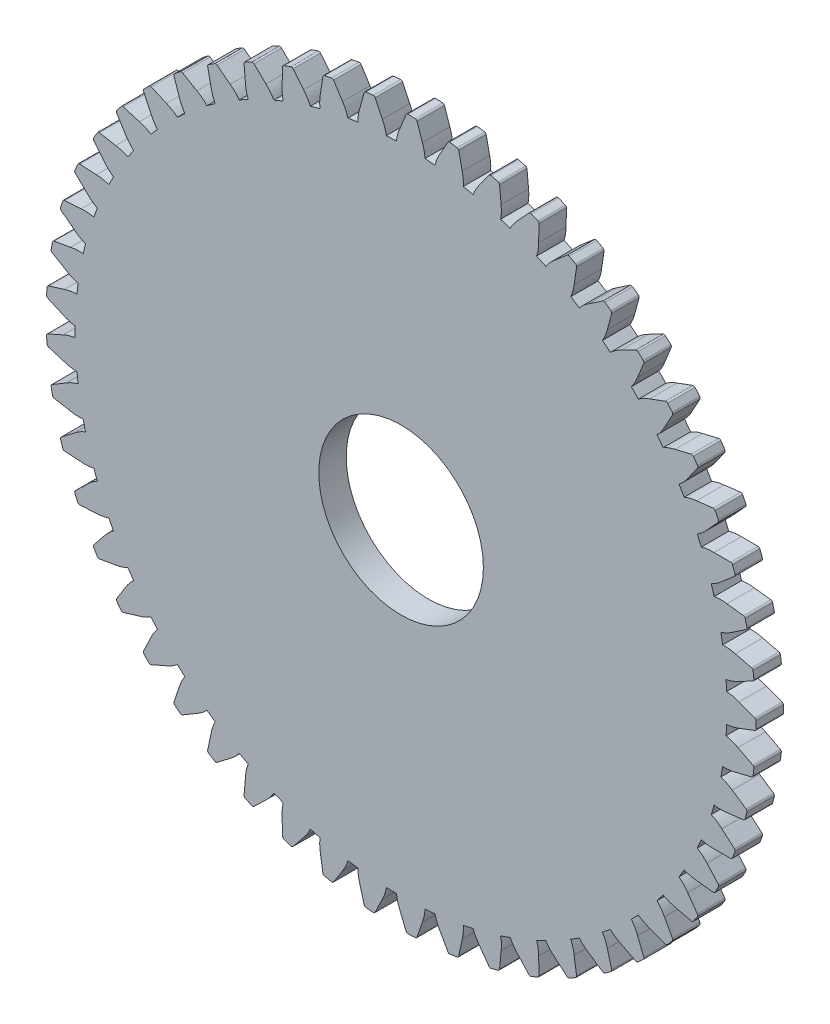
SolidWorks part; units mm, degrees
ref_plane "Front Plane" through (0, 0, 0) normal (0, 0, 1) x (1, 0, 0)
ref_plane "Top Plane" through (0, 0, 0) normal (0, 1, 0) x (1, 0, 0)
ref_plane "Right Plane" through (0, 0, 0) normal (1, 0, 0) x (0, 0, -1)
sketch "Model" plane through (0, 0, 0) normal (0, 0, 1) x (1, 0, 0)
  arc A0 (51.1069, 28.355) -> (51.0879, 28.7231) centre (27.376, 27.3159) ccw
  arc A1 (52.0104, 28.143) -> (51.1069, 28.355) centre (50.9075, 25.4735) ccw
  arc A2 (53.1489, 27.7177) -> (52.0104, 28.143) centre (-1532.1106, -4214.0875) ccw
  arc A3 (53.2463, 27.3159) -> (53.245, 27.5808) centre (27.376, 27.3159) ccw
  arc A4 (53.245, 27.5808) -> (53.1489, 27.7177) centre (53.0972, 27.5792) ccw
  arc A5 (51.0879, 25.9087) -> (51.1069, 26.2768) centre (27.376, 27.3159) ccw
  arc A6 (51.1069, 26.2768) -> (52.0104, 26.4888) centre (50.9075, 29.1583) ccw
  arc A7 (52.0104, 26.4888) -> (53.1489, 26.9141) centre (-1532.1106, 4268.7193) ccw
  arc A8 (53.245, 27.051) -> (53.2463, 27.3159) centre (27.376, 27.3159) ccw
  arc A9 (53.1489, 26.9141) -> (53.245, 27.051) centre (53.0972, 27.0525) ccw
  arc A10 (51.0633, 25.5409) -> (51.0879, 25.9087) centre (27.376, 27.3159) ccw
  arc A11 (51.9353, 25.2236) -> (51.0633, 25.5409) centre (50.5244, 22.7033) ccw
  arc A12 (53.0156, 24.6666) -> (51.9353, 25.2236) centre (-2022.8089, -3999.8721) ccw
  arc A13 (53.0647, 24.2561) -> (53.0947, 24.5193) centre (27.376, 27.3159) ccw
  arc A14 (53.0947, 24.5193) -> (53.0156, 24.6666) centre (52.9478, 24.5353) ccw
  arc A15 (50.7551, 23.1141) -> (50.8175, 23.4774) centre (27.376, 27.3159) ccw
  arc A16 (50.8175, 23.4774) -> (51.7396, 23.581) centre (50.9602, 26.3622) ccw
  arc A17 (51.7396, 23.581) -> (52.9205, 23.8687) centre (-1019.5204, 4423.3947) ccw
  arc A18 (53.0321, 23.9933) -> (53.0647, 24.2561) centre (27.376, 27.3159) ccw
  arc A19 (52.9205, 23.8687) -> (53.0321, 23.9933) centre (52.8855, 24.0123) ccw
  arc A20 (50.6871, 22.7518) -> (50.7551, 23.1141) centre (27.376, 27.3159) ccw
  arc A21 (51.5154, 22.3336) -> (50.6871, 22.7518) centre (49.8164, 19.9978) ccw
  arc A22 (52.5223, 21.6527) -> (51.5154, 22.3336) centre (-2484.7272, -3729.1238) ccw
  arc A23 (52.5226, 21.2393) -> (52.5834, 21.4971) centre (27.376, 27.3159) ccw
  arc A24 (52.5834, 21.4971) -> (52.5223, 21.6527) centre (52.4395, 21.5303) ccw
  arc A25 (50.094, 20.3785) -> (50.1989, 20.7318) centre (27.376, 27.3159) ccw
  arc A26 (50.1989, 20.7318) -> (51.1269, 20.7256) centre (50.6819, 23.5795) ccw
  arc A27 (51.1269, 20.7256) -> (52.3335, 20.8716) centre (-492.2342, 4516.3588) ccw
  arc A28 (52.459, 20.9822) -> (52.5226, 21.2393) centre (27.376, 27.3159) ccw
  arc A29 (52.3335, 20.8716) -> (52.459, 20.9822) centre (52.3157, 21.0183) ccw
  arc A30 (49.9836, 20.0268) -> (50.094, 20.3785) centre (27.376, 27.3159) ccw
  arc A31 (50.7567, 19.5135) -> (49.9836, 20.0268) centre (48.7933, 17.3951) ccw
  arc A32 (51.676, 18.7183) -> (50.7567, 19.5135) centre (-2911.381, -3405.6433) ccw
  arc A33 (51.6274, 18.3078) -> (51.7183, 18.5565) centre (27.376, 27.3159) ccw
  arc A34 (51.7183, 18.5565) -> (51.676, 18.7183) centre (51.5793, 18.6066) ccw
  arc A35 (49.1141, 17.7402) -> (49.26, 18.0787) centre (27.376, 27.3159) ccw
  arc A36 (49.26, 18.0787) -> (50.1807, 17.9628) centre (50.0764, 20.8493) ccw
  arc A37 (50.1807, 17.9628) -> (51.3962, 17.9651) centre (42.3462, 4546.3066) ccw
  arc A38 (51.5339, 18.06) -> (51.6274, 18.3078) centre (27.376, 27.3159) ccw
  arc A39 (51.3962, 17.9651) -> (51.5339, 18.06) centre (51.3959, 18.1128) ccw
  arc A40 (48.9629, 17.4041) -> (49.1141, 17.7402) centre (27.376, 27.3159) ccw
  arc A41 (49.6698, 16.8029) -> (48.9629, 17.4041) centre (47.4696, 14.9316) ccw
  arc A42 (50.4885, 15.9046) -> (49.6698, 16.8029) centre (-3296.7811, -3033.9716) ccw
  arc A43 (50.3917, 15.5027) -> (50.5115, 15.739) centre (27.376, 27.3159) ccw
  arc A44 (50.5115, 15.739) -> (50.4885, 15.9046) centre (50.3793, 15.8051) ccw
  arc A45 (47.8289, 15.2364) -> (48.0139, 15.5552) centre (27.376, 27.3159) ccw
  arc A46 (48.0139, 15.5552) -> (48.9144, 15.3313) centre (49.1522, 18.2098) ccw
  arc A47 (48.9144, 15.3313) -> (50.1216, 15.1898) centre (576.7165, 4512.8177) ccw
  arc A48 (50.2696, 15.2677) -> (50.3917, 15.5027) centre (27.376, 27.3159) ccw
  arc A49 (50.1216, 15.1898) -> (50.2696, 15.2677) centre (50.1388, 15.3365) ccw
  arc A50 (47.639, 14.9205) -> (47.8289, 15.2364) centre (27.376, 27.3159) ccw
  arc A51 (48.2699, 14.24) -> (47.639, 14.9205) centre (45.8639, 12.642) ccw
  arc A52 (48.9767, 13.2511) -> (48.2699, 14.24) centre (-3635.5173, -2619.3261) ccw
  arc A53 (48.833, 12.8635) -> (48.9798, 13.0839) centre (27.376, 27.3159) ccw
  arc A54 (48.9798, 13.0839) -> (48.9767, 13.2511) centre (48.8564, 13.1652) ccw
  arc A55 (46.2567, 12.9021) -> (46.4781, 13.1968) centre (27.376, 27.3159) ccw
  arc A56 (46.4781, 13.1968) -> (47.3458, 12.8679) centre (47.9224, 15.6982) ccw
  arc A57 (47.3458, 12.8679) -> (48.5278, 12.5847) centre (1103.3753, 4416.3621) ccw
  arc A58 (48.6839, 12.6446) -> (48.833, 12.8635) centre (27.376, 27.3159) ccw
  arc A59 (48.5278, 12.5847) -> (48.6839, 12.6446) centre (48.5622, 12.7284) ccw
  arc A60 (46.0308, 12.6109) -> (46.2567, 12.9021) centre (27.376, 27.3159) ccw
  arc A61 (46.5767, 11.8606) -> (46.0308, 12.6109) centre (43.9986, 10.5583) ccw
  arc A62 (47.1616, 10.7951) -> (46.5767, 11.8606) centre (-3922.8346, -2167.5276) ccw
  arc A63 (46.9731, 10.4271) -> (47.1449, 10.6287) centre (27.376, 27.3159) ccw
  arc A64 (47.1449, 10.6287) -> (47.1616, 10.7951) centre (47.032, 10.724) ccw
  arc A65 (44.4194, 10.7702) -> (44.6741, 11.0367) centre (27.376, 27.3159) ccw
  arc A66 (44.6741, 11.0367) -> (45.4968, 10.6075) centre (46.4041, 13.3497) ccw
  arc A67 (45.4968, 10.6075) -> (46.637, 10.1864) centre (1614.9294, 4258.294) ccw
  arc A68 (46.7991, 10.2274) -> (46.9731, 10.4271) centre (27.376, 27.3159) ccw
  arc A69 (46.637, 10.1864) -> (46.7991, 10.2274) centre (46.6882, 10.325) ccw
  arc A70 (44.1606, 10.5077) -> (44.4194, 10.7702) centre (27.376, 27.3159) ccw
  arc A71 (44.614, 9.6981) -> (44.1606, 10.5077) centre (41.8999, 8.71) ccw
  arc A72 (45.0687, 8.5709) -> (44.614, 9.6981) centre (-4154.6995, -1684.9183) ccw
  arc A73 (44.838, 8.2279) -> (45.0325, 8.4076) centre (27.376, 27.3159) ccw
  arc A74 (45.0325, 8.4076) -> (45.0687, 8.5709) centre (44.9317, 8.5157) ccw
  arc A75 (42.3429, 8.8706) -> (42.6273, 9.105) centre (27.376, 27.3159) ccw
  arc A76 (42.6273, 9.105) -> (43.3935, 8.5815) centre (44.6187, 11.1972) ccw
  arc A77 (43.3935, 8.5815) -> (44.4758, 8.0285) centre (2104.1977, 4040.8322) ccw
  arc A78 (44.6417, 8.0501) -> (44.838, 8.2279) centre (27.376, 27.3159) ccw
  arc A79 (44.4758, 8.0285) -> (44.6417, 8.0501) centre (44.5431, 8.1601) ccw
  arc A80 (42.0549, 8.6405) -> (42.3429, 8.8706) centre (27.376, 27.3159) ccw
  arc A81 (42.4093, 7.783) -> (42.0549, 8.6405) centre (39.5974, 7.1228) ccw
  arc A82 (42.7275, 6.6099) -> (42.4093, 7.783) centre (-4327.8573, -1178.2729) ccw
  arc A83 (42.4579, 6.2966) -> (42.6723, 6.4521) centre (27.376, 27.3159) ccw
  arc A84 (42.6723, 6.4521) -> (42.7275, 6.6099) centre (42.5849, 6.5712) ccw
  arc A85 (40.0562, 7.2299) -> (40.3664, 7.429) centre (27.376, 27.3159) ccw
  arc A86 (40.3664, 7.429) -> (41.0653, 6.8186) centre (42.5913, 9.2709) ccw
  arc A87 (41.0653, 6.8186) -> (42.0746, 6.1415) centre (2564.3119, 3767.0294) ccw
  arc A88 (42.2419, 6.1432) -> (42.4579, 6.2966) centre (27.376, 27.3159) ccw
  arc A89 (42.0746, 6.1415) -> (42.2419, 6.1432) centre (42.157, 6.2642) ccw
  arc A90 (39.743, 7.0355) -> (40.0562, 7.2299) centre (27.376, 27.3159) ccw
  arc A91 (39.9936, 6.142) -> (39.743, 7.0355) centre (37.1233, 5.819) ccw
  arc A92 (40.1708, 4.9396) -> (39.9936, 6.142) centre (-4439.8772, -654.7038) ccw
  arc A93 (39.866, 4.6603) -> (40.0973, 4.7894) centre (27.376, 27.3159) ccw
  arc A94 (40.0973, 4.7894) -> (40.1708, 4.9396) centre (40.0246, 4.918) ccw
  arc A95 (37.5916, 5.8711) -> (37.9231, 6.0322) centre (27.376, 27.3159) ccw
  arc A96 (37.9231, 6.0322) -> (38.5449, 5.3434) centre (40.3503, 7.598) ccw
  arc A97 (38.5449, 5.3434) -> (39.4671, 4.5516) centre (2988.8132, 3440.7292) ccw
  arc A98 (39.6334, 4.5336) -> (39.866, 4.6603) centre (27.376, 27.3159) ccw
  arc A99 (39.4671, 4.5516) -> (39.6334, 4.5336) centre (39.5634, 4.6637) ccw
  arc A100 (37.2576, 5.7152) -> (37.5916, 5.8711) centre (27.376, 27.3159) ccw
  arc A101 (37.4007, 4.7983) -> (37.2576, 5.7152) centre (34.5124, 4.8171) ccw
  arc A102 (37.4345, 3.5833) -> (37.4007, 4.7983) centre (-4489.1866, -121.5606) ccw
  arc A103 (37.0988, 3.3421) -> (37.3437, 3.4429) centre (27.376, 27.3159) ccw
  arc A104 (37.3437, 3.4429) -> (37.4345, 3.5833) centre (37.2868, 3.5792) ccw
  arc A105 (34.9836, 4.8134) -> (35.3318, 4.9341) centre (27.376, 27.3159) ccw
  arc A106 (35.3318, 4.9341) -> (35.8678, 4.1766) centre (37.9271, 6.2019) ccw
  arc A107 (35.8678, 4.1766) -> (36.6898, 3.2813) centre (3371.7424, 3066.5122) ccw
  arc A108 (36.8528, 3.2438) -> (37.0988, 3.3421) centre (27.376, 27.3159) ccw
  arc A109 (36.6898, 3.2813) -> (36.8528, 3.2438) centre (36.7987, 3.3813) ccw
  arc A110 (34.6335, 4.698) -> (34.9836, 4.8134) centre (27.376, 27.3159) ccw
  arc A111 (34.6671, 3.7707) -> (34.6335, 4.698) centre (31.8013, 4.1309) ccw
  arc A112 (34.5569, 2.5603) -> (34.6671, 3.7707) centre (-4475.0933, 413.6726) ccw
  arc A113 (34.1951, 2.3604) -> (34.4502, 2.4315) centre (27.376, 27.3159) ccw
  arc A114 (34.4502, 2.4315) -> (34.5569, 2.5603) centre (34.4098, 2.5737) ccw
  arc A115 (32.2687, 4.0715) -> (32.6288, 4.1503) centre (27.376, 27.3159) ccw
  arc A116 (32.6288, 4.1503) -> (33.0714, 3.3347) centre (35.3558, 5.1022) ccw
  arc A117 (33.0714, 3.3347) -> (33.7818, 2.3484) centre (3707.724, 2649.6316) ccw
  arc A118 (33.9392, 2.2919) -> (34.1951, 2.3604) centre (27.376, 27.3159) ccw
  arc A119 (33.7818, 2.3484) -> (33.9392, 2.2919) centre (33.9017, 2.4348) ccw
  arc A120 (31.9074, 3.9984) -> (32.2687, 4.0715) centre (27.376, 27.3159) ccw
  arc A121 (31.8312, 3.0736) -> (31.9074, 3.9984) centre (29.0281, 3.7703) ccw
  arc A122 (31.5786, 1.8847) -> (31.8312, 3.0736) centre (-4397.7953, 943.4821) ccw
  arc A123 (31.1956, 1.7291) -> (31.4574, 1.7695) centre (27.376, 27.3159) ccw
  arc A124 (31.4574, 1.7695) -> (31.5786, 1.8847) centre (31.4341, 1.9154) ccw
  arc A125 (29.4852, 3.656) -> (29.8521, 3.6916) centre (27.376, 27.3159) ccw
  arc A126 (29.8521, 3.6916) -> (30.1951, 2.8294) centre (32.6725, 4.3143) ccw
  arc A127 (30.1951, 2.8294) -> (30.7839, 1.7661) centre (3992.0416, 2195.9394) ccw
  arc A128 (30.9335, 1.6913) -> (31.1956, 1.7291) centre (27.376, 27.3159) ccw
  arc A129 (30.7839, 1.7661) -> (30.9335, 1.6913) centre (30.9131, 1.8377) ccw
  arc A130 (29.1178, 3.6261) -> (29.4852, 3.656) centre (27.376, 27.3159) ccw
  arc A131 (28.9327, 2.7168) -> (29.1178, 3.6261) centre (26.2317, 3.7401) ccw
  arc A132 (28.5413, 1.5661) -> (28.9327, 2.7168) centre (-4258.3776, 1460.4306) ccw
  arc A133 (28.1426, 1.4569) -> (28.4073, 1.4661) centre (27.376, 27.3159) ccw
  arc A134 (28.4073, 1.4661) -> (28.5413, 1.5661) centre (28.4014, 1.6137) ccw
  arc A135 (26.6721, 3.5726) -> (27.0406, 3.5646) centre (27.376, 27.3159) ccw
  arc A136 (27.0406, 3.5646) -> (27.2792, 2.6678) centre (29.9149, 3.8493) ccw
  arc A137 (27.2792, 2.6678) -> (27.7381, 1.5423) centre (4220.7039, 1711.8044) ccw
  arc A138 (27.8778, 1.4504) -> (28.1426, 1.4569) centre (27.376, 27.3159) ccw
  arc A139 (27.7381, 1.5423) -> (27.8778, 1.4504) centre (27.8749, 1.5981) ccw
  arc A140 (26.3037, 3.5864) -> (26.6721, 3.5726) centre (27.376, 27.3159) ccw
  arc A141 (26.0124, 2.7054) -> (26.3037, 3.5864) centre (23.4513, 4.0409) ccw
  arc A142 (25.4876, 1.609) -> (26.0124, 2.7054) centre (-4058.7973, 1957.2614) ccw
  arc A143 (25.0788, 1.5477) -> (25.3427, 1.5255) centre (27.376, 27.3159) ccw
  arc A144 (25.3427, 1.5255) -> (25.4876, 1.609) centre (25.3543, 1.6729) ccw
  arc A145 (23.8688, 3.8225) -> (24.2338, 3.7709) centre (27.376, 27.3159) ccw
  arc A146 (24.2338, 3.7709) -> (24.3647, 2.8522) centre (27.1216, 3.7137) ccw
  arc A147 (24.3647, 2.8522) -> (24.6872, 1.6804) centre (4390.5012, 1204.023) ccw
  arc A148 (24.8151, 1.5726) -> (25.0788, 1.5477) centre (27.376, 27.3159) ccw
  arc A149 (24.6872, 1.6804) -> (24.8151, 1.5726) centre (24.8297, 1.7196) ccw
  arc A150 (23.5047, 3.8798) -> (23.8688, 3.8225) centre (27.376, 27.3159) ccw
  arc A151 (23.1112, 3.0394) -> (23.5047, 3.8798) centre (20.7261, 4.6685) ccw
  arc A152 (22.4604, 2.0128) -> (23.1112, 3.0394) centre (-3801.856, 2427) ccw
  arc A153 (22.0472, 2.0003) -> (22.3067, 1.947) centre (27.376, 27.3159) ccw
  arc A154 (22.3067, 1.947) -> (22.4604, 2.0128) centre (22.3356, 2.0919) ccw
  arc A155 (21.1148, 4.4022) -> (21.4711, 4.3078) centre (27.376, 27.3159) ccw
  arc A156 (21.4711, 4.3078) -> (21.4924, 3.3801) centre (24.3319, 3.9095) ccw
  arc A157 (21.4924, 3.3801) -> (21.6741, 2.1783) centre (4499.0497, 679.7231) ccw
  arc A158 (21.7883, 2.0562) -> (22.0472, 2.0003) centre (27.376, 27.3159) ccw
  arc A159 (21.6741, 2.1783) -> (21.7883, 2.0562) centre (21.8202, 2.2004) ccw
  arc A160 (20.76, 4.5021) -> (21.1148, 4.4022) centre (27.376, 27.3159) ccw
  arc A161 (20.2698, 3.7142) -> (20.76, 4.5021) centre (18.0942, 5.6139) ccw
  arc A162 (19.5023, 2.7718) -> (20.2698, 3.7142) centre (-3491.1608, 2863.0522) ccw
  arc A163 (19.0905, 2.8082) -> (19.3418, 2.7247) centre (27.376, 27.3159) ccw
  arc A164 (19.3418, 2.7247) -> (19.5023, 2.7718) centre (19.3877, 2.8651) ccw
  arc A165 (18.4487, 5.3036) -> (18.7913, 5.1677) centre (27.376, 27.3159) ccw
  arc A166 (18.7913, 5.1677) -> (18.7028, 4.244) centre (21.5849, 4.4338) ccw
  arc A167 (18.7028, 4.244) -> (18.741, 3.0291) centre (4544.8257, 146.2649) ccw
  arc A168 (18.84, 2.8943) -> (19.0905, 2.8082) centre (27.376, 27.3159) ccw
  arc A169 (18.741, 3.0291) -> (18.84, 2.8943) centre (18.8887, 3.0338) ccw
  arc A170 (18.1082, 5.4448) -> (18.4487, 5.3036) centre (27.376, 27.3159) ccw
  arc A171 (17.5283, 4.7203) -> (18.1082, 5.4448) centre (15.5925, 6.8641) ccw
  arc A172 (16.6546, 3.8753) -> (17.5283, 4.7203) centre (-3131.073, 3259.297) ccw
  arc A173 (16.25, 3.9602) -> (16.4897, 3.8475) centre (27.376, 27.3159) ccw
  arc A174 (16.4897, 3.8475) -> (16.6546, 3.8753) centre (16.5519, 3.9815) ccw
  arc A175 (15.9079, 6.5139) -> (16.232, 6.3385) centre (27.376, 27.3159) ccw
  arc A176 (16.232, 6.3385) -> (16.0348, 5.4317) centre (18.9192, 5.2793) ccw
  arc A177 (16.0348, 5.4317) -> (15.9292, 4.2209) centre (4527.1867, -388.8631) ccw
  arc A178 (16.0115, 4.0753) -> (16.25, 3.9602) centre (27.376, 27.3159) ccw
  arc A179 (15.9292, 4.2209) -> (16.0115, 4.0753) centre (16.0764, 4.2081) ccw
  arc A180 (15.5864, 6.6944) -> (15.9079, 6.5139) centre (27.376, 27.3159) ccw
  arc A181 (14.9249, 6.0436) -> (15.5864, 6.6944) centre (13.2563, 8.4013) ccw
  arc A182 (13.9575, 5.3079) -> (14.9249, 6.0436) centre (-2726.6475, 3610.1718) ccw
  arc A183 (13.5657, 5.44) -> (13.7904, 5.2998) centre (27.376, 27.3159) ccw
  arc A184 (13.7904, 5.2998) -> (13.9575, 5.3079) centre (13.868, 5.4255) ccw
  arc A185 (13.528, 8.0163) -> (13.8292, 7.8038) centre (27.376, 27.3159) ccw
  arc A186 (13.8292, 7.8038) -> (13.5261, 6.9267) centre (16.3722, 6.4342) ccw
  arc A187 (13.5261, 6.9267) -> (13.278, 5.7368) centre (4446.3801, -918.1488) ccw
  arc A188 (13.3425, 5.5825) -> (13.5657, 5.44) centre (27.376, 27.3159) ccw
  arc A189 (13.278, 5.7368) -> (13.3425, 5.5825) centre (13.4227, 5.7067) ccw
  arc A190 (13.2302, 8.2335) -> (13.528, 8.0163) centre (27.376, 27.3159) ccw
  arc A191 (12.4964, 7.6655) -> (13.2302, 8.2335) centre (11.1184, 10.204) ccw
  arc A192 (11.4487, 7.0494) -> (12.4964, 7.6655) centre (-2283.5615, 3910.7511) ccw
  arc A193 (11.0754, 7.2269) -> (11.2819, 7.0611) centre (27.376, 27.3159) ccw
  arc A194 (11.2819, 7.0611) -> (11.4487, 7.0494) centre (11.3738, 7.1768) ccw
  arc A195 (11.3426, 9.7896) -> (11.6165, 9.5429) centre (27.376, 27.3159) ccw
  arc A196 (11.6165, 9.5429) -> (11.2119, 8.7078) centre (13.9797, 7.8822) ccw
  arc A197 (11.2119, 8.7078) -> (10.8247, 7.5557) centre (4303.5404, -1434.1624) ccw
  arc A198 (10.8705, 7.3949) -> (11.0754, 7.2269) centre (27.376, 27.3159) ccw
  arc A199 (10.8247, 7.5557) -> (10.8705, 7.3949) centre (10.9648, 7.5087) ccw
  arc A200 (11.0726, 10.0405) -> (11.3426, 9.7896) centre (27.376, 27.3159) ccw
  arc A201 (10.2767, 9.5633) -> (11.0726, 10.0405) centre (9.2086, 12.2469) ccw
  arc A202 (9.1635, 9.0754) -> (10.2767, 9.5633) centre (-1808.0351, 4156.8156) ccw
  arc A203 (8.8138, 9.2959) -> (8.9992, 9.1068) centre (27.376, 27.3159) ccw
  arc A204 (8.9992, 9.1068) -> (9.1635, 9.0754) centre (9.1042, 9.2108) ccw
  arc A205 (9.3823, 11.8089) -> (9.6251, 11.5316) centre (27.376, 27.3159) ccw
  arc A206 (9.6251, 11.5316) -> (9.1245, 10.7502) centre (11.7753, 9.603) ccw
  arc A207 (9.1245, 10.7502) -> (8.6038, 9.652) centre (4100.6728, -1929.6599) ccw
  arc A208 (8.6303, 9.4868) -> (8.8138, 9.2959) centre (27.376, 27.3159) ccw
  arc A209 (8.6038, 9.652) -> (8.6303, 9.4868) centre (8.7373, 9.5887) ccw
  arc A210 (9.1438, 12.09) -> (9.3823, 11.8089) centre (27.376, 27.3159) ccw
  arc A211 (8.2971, 11.7103) -> (9.1438, 12.09) centre (7.5539, 14.5014) ccw
  arc A212 (7.134, 11.3575) -> (8.2971, 11.7103) centre (-1306.7435, 4344.9109) ccw
  arc A213 (6.8128, 11.6177) -> (6.9746, 11.408) centre (27.376, 27.3159) ccw
  arc A214 (6.9746, 11.408) -> (7.134, 11.3575) centre (7.0911, 11.4989) ccw
  arc A215 (7.6745, 14.046) -> (7.8828, 13.7418) centre (27.376, 27.3159) ccw
  arc A216 (7.8828, 13.7418) -> (7.2933, 13.0252) centre (9.7898, 11.5725) ccw
  arc A217 (7.2933, 13.0252) -> (6.6464, 11.9962) centre (3840.625, -2397.6858) ccw
  arc A218 (6.6531, 11.8291) -> (6.8128, 11.6177) centre (27.376, 27.3159) ccw
  arc A219 (6.6464, 11.9962) -> (6.6531, 11.8291) centre (6.7715, 11.9176) ccw
  arc A220 (7.471, 14.3533) -> (7.6745, 14.046) centre (27.376, 27.3159) ccw
  arc A221 (6.5853, 14.0763) -> (7.471, 14.3533) centre (6.1774, 16.9358) ccw
  arc A222 (5.3886, 13.8636) -> (6.5853, 14.0763) centre (-786.7238, 4472.3966) ccw
  arc A223 (5.1004, 14.16) -> (5.2363, 13.9326) centre (27.376, 27.3159) ccw
  arc A224 (5.2363, 13.9326) -> (5.3886, 13.8636) centre (5.3628, 14.0091) ccw
  arc A225 (6.2433, 16.4693) -> (6.4142, 16.1426) centre (27.376, 27.3159) ccw
  arc A226 (6.4142, 16.1426) -> (5.7441, 15.5007) centre (8.0512, 13.763) ccw
  arc A227 (5.7441, 15.5007) -> (4.98, 14.5555) centre (3527.0475, -2831.67) ccw
  arc A228 (4.9669, 14.3887) -> (5.1004, 14.16) centre (27.376, 27.3159) ccw
  arc A229 (4.98, 14.5555) -> (4.9669, 14.3887) centre (5.0949, 14.4626) ccw
  arc A230 (6.0775, 16.7985) -> (6.2433, 16.4693) centre (27.376, 27.3159) ccw
  arc A231 (5.1653, 16.6283) -> (6.0775, 16.7985) centre (5.0985, 19.5159) ccw
  arc A232 (3.9519, 16.5585) -> (5.1653, 16.6283) centre (-255.2759, 4537.4832) ccw
  arc A233 (3.7008, 16.8869) -> (3.8088, 16.6451) centre (27.376, 27.3159) ccw
  arc A234 (3.8088, 16.6451) -> (3.9519, 16.5585) centre (3.9434, 16.706) ccw
  arc A235 (5.1088, 19.0448) -> (5.2398, 18.7003) centre (27.376, 27.3159) ccw
  arc A236 (5.2398, 18.7003) -> (4.4985, 18.1421) centre (6.5839, 16.1437) ccw
  arc A237 (4.4985, 18.1421) -> (3.628, 17.2939) centre (3164.3423, -3225.5203) ccw
  arc A238 (3.5953, 17.1299) -> (3.7008, 16.8869) centre (27.376, 27.3159) ccw
  arc A239 (3.628, 17.2939) -> (3.5953, 17.1299) centre (3.7311, 17.1881) ccw
  arc A240 (4.9831, 19.3913) -> (5.1088, 19.0448) centre (27.376, 27.3159) ccw
  arc A241 (4.0572, 19.3302) -> (4.9831, 19.3913) centre (4.3323, 22.2054) ccw
  arc A242 (2.844, 19.4045) -> (4.0572, 19.3302) centre (280.1398, 4539.2569) ccw
  arc A243 (2.6335, 19.7603) -> (2.7122, 19.5073) centre (27.376, 27.3159) ccw
  arc A244 (2.7122, 19.5073) -> (2.844, 19.4045) centre (2.853, 19.552) ccw
  arc A245 (4.2868, 21.7365) -> (4.3762, 21.3789) centre (27.376, 27.3159) ccw
  arc A246 (4.3762, 21.3789) -> (3.574, 20.9123) centre (5.4085, 18.6813) ccw
  arc A247 (3.574, 20.9123) -> (2.6093, 20.173) centre (2757.601, -3573.7079) ccw
  arc A248 (2.5575, 20.014) -> (2.6335, 19.7603) centre (27.376, 27.3159) ccw
  arc A249 (2.6093, 20.173) -> (2.5575, 20.014) centre (2.6992, 20.0557) ccw
  arc A250 (4.203, 22.0954) -> (4.2868, 21.7365) centre (27.376, 27.3159) ccw
  arc A251 (3.2763, 22.1442) -> (4.203, 22.0954) centre (3.8896, 24.9668) ccw
  arc A252 (2.0805, 22.3615) -> (3.2763, 22.1442) centre (812.0073, 4477.6928) ccw
  arc A253 (1.9135, 22.7397) -> (1.9617, 22.4792) centre (27.376, 27.3159) ccw
  arc A254 (1.9617, 22.4792) -> (2.0805, 22.3615) centre (2.1069, 22.5068) ccw
  arc A255 (3.789, 24.5065) -> (3.8354, 24.1408) centre (27.376, 27.3159) ccw
  arc A256 (3.8354, 24.1408) -> (2.9837, 23.7724) centre (4.5414, 21.34) ccw
  arc A257 (2.9837, 23.7724) -> (1.9383, 23.1523) centre (2312.5333, -3871.3451) ccw
  arc A258 (1.868, 23.0006) -> (1.9135, 22.7397) centre (27.376, 27.3159) ccw
  arc A259 (1.9383, 23.1523) -> (1.868, 23.0006) centre (2.0137, 23.0252) ccw
  arc A260 (3.7482, 24.8728) -> (3.789, 24.5065) centre (27.376, 27.3159) ccw
  arc A261 (2.8338, 25.0309) -> (3.7482, 24.8728) centre (3.7766, 27.7611) ccw
  arc A262 (1.672, 25.388) -> (2.8338, 25.0309) centre (1332.8602, 4353.6552) ccw
  arc A263 (1.551, 25.7833) -> (1.5681, 25.519) centre (27.376, 27.3159) ccw
  arc A264 (1.5681, 25.519) -> (1.672, 25.388) centre (1.7155, 25.5293) ccw
  arc A265 (3.6223, 27.3159) -> (3.6251, 26.9473) centre (27.376, 27.3159) ccw
  arc A266 (3.6251, 26.9473) -> (2.7358, 26.6822) centre (3.9949, 24.0827) ccw
  arc A267 (2.7358, 26.6822) -> (1.6244, 26.1901) centre (1835.387, -4114.2535) ccw
  arc A268 (1.5367, 26.0478) -> (1.551, 25.7833) centre (27.376, 27.3159) ccw
  arc A269 (1.6244, 26.1901) -> (1.5367, 26.0478) centre (1.6843, 26.055) ccw
  arc A270 (3.6251, 27.6845) -> (3.6223, 27.3159) centre (27.376, 27.3159) ccw
  arc A271 (2.7358, 27.9496) -> (3.6251, 27.6845) centre (3.9949, 30.5491) ccw
  arc A272 (1.6244, 28.4416) -> (2.7358, 27.9496) centre (1835.387, 4168.8853) ccw
  arc A273 (1.551, 28.8485) -> (1.5367, 28.584) centre (27.376, 27.3159) ccw
  arc A274 (1.5367, 28.584) -> (1.6244, 28.4416) centre (1.6843, 28.5767) ccw
  arc A275 (3.789, 30.1253) -> (3.7482, 29.759) centre (27.376, 27.3159) ccw
  arc A276 (3.7482, 29.759) -> (2.8338, 29.6009) centre (3.7766, 26.8707) ccw
  arc A277 (2.8338, 29.6009) -> (1.672, 29.2438) centre (1332.8602, -4299.0235) ccw
  arc A278 (1.5681, 29.1128) -> (1.551, 28.8485) centre (27.376, 27.3159) ccw
  arc A279 (1.672, 29.2438) -> (1.5681, 29.1128) centre (1.7155, 29.1025) ccw
  arc A280 (3.8354, 30.491) -> (3.789, 30.1253) centre (27.376, 27.3159) ccw
  arc A281 (2.9837, 30.8594) -> (3.8354, 30.491) centre (4.5414, 33.2917) ccw
  arc A282 (1.9383, 31.4794) -> (2.9837, 30.8594) centre (2312.5333, 3925.9768) ccw
  arc A283 (1.9135, 31.8921) -> (1.868, 31.6312) centre (27.376, 27.3159) ccw
  arc A284 (1.868, 31.6312) -> (1.9383, 31.4794) centre (2.0137, 31.6065) ccw
  arc A285 (4.2868, 32.8953) -> (4.203, 32.5364) centre (27.376, 27.3159) ccw
  arc A286 (4.203, 32.5364) -> (3.2763, 32.4875) centre (3.8896, 29.665) ccw
  arc A287 (3.2763, 32.4875) -> (2.0805, 32.2703) centre (812.0073, -4423.0611) ccw
  arc A288 (1.9617, 32.1526) -> (1.9135, 31.8921) centre (27.376, 27.3159) ccw
  arc A289 (2.0805, 32.2703) -> (1.9617, 32.1526) centre (2.1069, 32.1249) ccw
  arc A290 (4.3762, 33.2529) -> (4.2868, 32.8953) centre (27.376, 27.3159) ccw
  arc A291 (3.574, 33.7195) -> (4.3762, 33.2529) centre (5.4085, 35.9505) ccw
  arc A292 (2.6093, 34.4588) -> (3.574, 33.7195) centre (2757.601, 3628.3397) ccw
  arc A293 (2.6335, 34.8715) -> (2.5575, 34.6178) centre (27.376, 27.3159) ccw
  arc A294 (2.5575, 34.6178) -> (2.6093, 34.4588) centre (2.6992, 34.5761) ccw
  arc A295 (5.1088, 35.587) -> (4.9831, 35.2404) centre (27.376, 27.3159) ccw
  arc A296 (4.9831, 35.2404) -> (4.0572, 35.3016) centre (4.3323, 32.4263) ccw
  arc A297 (4.0572, 35.3016) -> (2.844, 35.2273) centre (280.1398, -4484.6251) ccw
  arc A298 (2.7122, 35.1244) -> (2.6335, 34.8715) centre (27.376, 27.3159) ccw
  arc A299 (2.844, 35.2273) -> (2.7122, 35.1244) centre (2.853, 35.0798) ccw
  arc A300 (5.2398, 35.9315) -> (5.1088, 35.587) centre (27.376, 27.3159) ccw
  arc A301 (4.4985, 36.4897) -> (5.2398, 35.9315) centre (6.5839, 38.4881) ccw
  arc A302 (3.628, 37.3379) -> (4.4985, 36.4897) centre (3164.3423, 3280.1521) ccw
  arc A303 (3.7008, 37.7448) -> (3.5953, 37.5019) centre (27.376, 27.3159) ccw
  arc A304 (3.5953, 37.5019) -> (3.628, 37.3379) centre (3.7311, 37.4437) ccw
  arc A305 (6.2433, 38.1625) -> (6.0775, 37.8333) centre (27.376, 27.3159) ccw
  arc A306 (6.0775, 37.8333) -> (5.1653, 38.0035) centre (5.0985, 35.1159) ccw
  arc A307 (5.1653, 38.0035) -> (3.9519, 38.0733) centre (-255.2759, -4482.8514) ccw
  arc A308 (3.8088, 37.9867) -> (3.7008, 37.7448) centre (27.376, 27.3159) ccw
  arc A309 (3.9519, 38.0733) -> (3.8088, 37.9867) centre (3.9434, 37.9257) ccw
  arc A310 (6.4142, 38.4891) -> (6.2433, 38.1625) centre (27.376, 27.3159) ccw
  arc A311 (5.7441, 39.1311) -> (6.4142, 38.4891) centre (8.0512, 40.8688) ccw
  arc A312 (4.98, 40.0763) -> (5.7441, 39.1311) centre (3527.0475, 2886.3018) ccw
  arc A313 (5.1004, 40.4718) -> (4.9669, 40.243) centre (27.376, 27.3159) ccw
  arc A314 (4.9669, 40.243) -> (4.98, 40.0763) centre (5.0949, 40.1692) ccw
  arc A315 (7.6745, 40.5858) -> (7.471, 40.2785) centre (27.376, 27.3159) ccw
  arc A316 (7.471, 40.2785) -> (6.5853, 40.5554) centre (6.1774, 37.696) ccw
  arc A317 (6.5853, 40.5554) -> (5.3886, 40.7682) centre (-786.7238, -4417.7649) ccw
  arc A318 (5.2363, 40.6991) -> (5.1004, 40.4718) centre (27.376, 27.3159) ccw
  arc A319 (5.3886, 40.7682) -> (5.2363, 40.6991) centre (5.3628, 40.6227) ccw
  arc A320 (7.8828, 40.8899) -> (7.6745, 40.5858) centre (27.376, 27.3159) ccw
  arc A321 (7.2933, 41.6066) -> (7.8828, 40.8899) centre (9.7898, 43.0593) ccw
  arc A322 (6.6464, 42.6356) -> (7.2933, 41.6066) centre (3840.625, 2452.3176) ccw
  arc A323 (6.8128, 43.014) -> (6.6531, 42.8027) centre (27.376, 27.3159) ccw
  arc A324 (6.6531, 42.8027) -> (6.6464, 42.6356) centre (6.7715, 42.7142) ccw
  arc A325 (9.3823, 42.8228) -> (9.1438, 42.5418) centre (27.376, 27.3159) ccw
  arc A326 (9.1438, 42.5418) -> (8.2971, 42.9215) centre (7.5539, 40.1304) ccw
  arc A327 (8.2971, 42.9215) -> (7.134, 43.2743) centre (-1306.7435, -4290.2791) ccw
  arc A328 (6.9746, 43.2237) -> (6.8128, 43.014) centre (27.376, 27.3159) ccw
  arc A329 (7.134, 43.2743) -> (6.9746, 43.2237) centre (7.0911, 43.1329) ccw
  arc A330 (9.6251, 43.1002) -> (9.3823, 42.8228) centre (27.376, 27.3159) ccw
  arc A331 (9.1245, 43.8815) -> (9.6251, 43.1002) centre (11.7753, 45.0287) ccw
  arc A332 (8.6038, 44.9798) -> (9.1245, 43.8815) centre (4100.6728, 1984.2917) ccw
  arc A333 (8.8138, 45.3359) -> (8.6303, 45.1449) centre (27.376, 27.3159) ccw
  arc A334 (8.6303, 45.1449) -> (8.6038, 44.9798) centre (8.7373, 45.0431) ccw
  arc A335 (11.3426, 44.8422) -> (11.0726, 44.5913) centre (27.376, 27.3159) ccw
  arc A336 (11.0726, 44.5913) -> (10.2767, 45.0685) centre (9.2086, 42.3848) ccw
  arc A337 (10.2767, 45.0685) -> (9.1635, 45.5564) centre (-1808.0351, -4102.1838) ccw
  arc A338 (8.9992, 45.525) -> (8.8138, 45.3359) centre (27.376, 27.3159) ccw
  arc A339 (9.1635, 45.5564) -> (8.9992, 45.525) centre (9.1042, 45.421) ccw
  arc A340 (11.6165, 45.0888) -> (11.3426, 44.8422) centre (27.376, 27.3159) ccw
  arc A341 (11.2119, 45.9239) -> (11.6165, 45.0888) centre (13.9797, 46.7495) ccw
  arc A342 (10.8247, 47.0761) -> (11.2119, 45.9239) centre (4303.5404, 1488.7941) ccw
  arc A343 (11.0754, 47.4048) -> (10.8705, 47.2369) centre (27.376, 27.3159) ccw
  arc A344 (10.8705, 47.2369) -> (10.8247, 47.0761) centre (10.9648, 47.1231) ccw
  arc A345 (13.528, 46.6155) -> (13.2302, 46.3983) centre (27.376, 27.3159) ccw
  arc A346 (13.2302, 46.3983) -> (12.4964, 46.9662) centre (11.1184, 44.4278) ccw
  arc A347 (12.4964, 46.9662) -> (11.4487, 47.5824) centre (-2283.5615, -3856.1193) ccw
  arc A348 (11.2819, 47.5707) -> (11.0754, 47.4048) centre (27.376, 27.3159) ccw
  arc A349 (11.4487, 47.5824) -> (11.2819, 47.5707) centre (11.3738, 47.455) ccw
  arc A350 (13.8292, 46.828) -> (13.528, 46.6155) centre (27.376, 27.3159) ccw
  arc A351 (13.5261, 47.7051) -> (13.8292, 46.828) centre (16.3722, 48.1976) ccw
  arc A352 (13.278, 48.8949) -> (13.5261, 47.7051) centre (4446.3801, 972.7806) ccw
  arc A353 (13.5657, 49.1918) -> (13.3425, 49.0492) centre (27.376, 27.3159) ccw
  arc A354 (13.3425, 49.0492) -> (13.278, 48.8949) centre (13.4227, 48.9251) ccw
  arc A355 (15.9079, 48.1178) -> (15.5864, 47.9374) centre (27.376, 27.3159) ccw
  arc A356 (15.5864, 47.9374) -> (14.9249, 48.5882) centre (13.2563, 46.2305) ccw
  arc A357 (14.9249, 48.5882) -> (13.9575, 49.3239) centre (-2726.6475, -3555.54) ccw
  arc A358 (13.7904, 49.332) -> (13.5657, 49.1918) centre (27.376, 27.3159) ccw
  arc A359 (13.9575, 49.3239) -> (13.7904, 49.332) centre (13.868, 49.2063) ccw
  arc A360 (16.232, 48.2933) -> (15.9079, 48.1178) centre (27.376, 27.3159) ccw
  arc A361 (16.0348, 49.2001) -> (16.232, 48.2933) centre (18.9192, 49.3524) ccw
  arc A362 (15.9292, 50.4109) -> (16.0348, 49.2001) centre (4527.1867, 443.4949) ccw
  arc A363 (16.25, 50.6716) -> (16.0115, 50.5565) centre (27.376, 27.3159) ccw
  arc A364 (16.0115, 50.5565) -> (15.9292, 50.4109) centre (16.0764, 50.4237) ccw
  arc A365 (18.4487, 49.3282) -> (18.1082, 49.187) centre (27.376, 27.3159) ccw
  arc A366 (18.1082, 49.187) -> (17.5283, 49.9115) centre (15.5925, 47.7677) ccw
  arc A367 (17.5283, 49.9115) -> (16.6546, 50.7565) centre (-3131.073, -3204.6652) ccw
  arc A368 (16.4897, 50.7843) -> (16.25, 50.6716) centre (27.376, 27.3159) ccw
  arc A369 (16.6546, 50.7565) -> (16.4897, 50.7843) centre (16.5519, 50.6502) ccw
  arc A370 (18.7913, 49.4641) -> (18.4487, 49.3282) centre (27.376, 27.3159) ccw
  arc A371 (18.7028, 50.3878) -> (18.7913, 49.4641) centre (21.5849, 50.198) ccw
  arc A372 (18.741, 51.6026) -> (18.7028, 50.3878) centre (4544.8257, -91.6331) ccw
  arc A373 (19.0905, 51.8236) -> (18.84, 51.7375) centre (27.376, 27.3159) ccw
  arc A374 (18.84, 51.7375) -> (18.741, 51.6026) centre (18.8887, 51.598) ccw
  arc A375 (21.1148, 50.2296) -> (20.76, 50.1296) centre (27.376, 27.3159) ccw
  arc A376 (20.76, 50.1296) -> (20.2698, 50.9176) centre (18.0942, 49.0178) ccw
  arc A377 (20.2698, 50.9176) -> (19.5023, 51.86) centre (-3491.1608, -2808.4204) ccw
  arc A378 (19.3418, 51.9071) -> (19.0905, 51.8236) centre (27.376, 27.3159) ccw
  arc A379 (19.5023, 51.86) -> (19.3418, 51.9071) centre (19.3877, 51.7666) ccw
  arc A380 (21.4711, 50.324) -> (21.1148, 50.2296) centre (27.376, 27.3159) ccw
  arc A381 (21.4924, 51.2517) -> (21.4711, 50.324) centre (24.3319, 50.7223) ccw
  arc A382 (21.6741, 52.4534) -> (21.4924, 51.2517) centre (4499.0497, -625.0914) ccw
  arc A383 (22.0472, 52.6315) -> (21.7883, 52.5756) centre (27.376, 27.3159) ccw
  arc A384 (21.7883, 52.5756) -> (21.6741, 52.4534) centre (21.8202, 52.4313) ccw
  arc A385 (23.8688, 50.8093) -> (23.5047, 50.752) centre (27.376, 27.3159) ccw
  arc A386 (23.5047, 50.752) -> (23.1112, 51.5924) centre (20.7261, 49.9633) ccw
  arc A387 (23.1112, 51.5924) -> (22.4604, 52.619) centre (-3801.856, -2372.3682) ccw
  arc A388 (22.3067, 52.6847) -> (22.0472, 52.6315) centre (27.376, 27.3159) ccw
  arc A389 (22.4604, 52.619) -> (22.3067, 52.6847) centre (22.3356, 52.5398) ccw
  arc A390 (24.2338, 50.8608) -> (23.8688, 50.8093) centre (27.376, 27.3159) ccw
  arc A391 (24.3647, 51.7795) -> (24.2338, 50.8608) centre (27.1216, 50.918) ccw
  arc A392 (24.6872, 52.9514) -> (24.3647, 51.7795) centre (4390.5012, -1149.3912) ccw
  arc A393 (25.0788, 53.0841) -> (24.8151, 53.0592) centre (27.376, 27.3159) ccw
  arc A394 (24.8151, 53.0592) -> (24.6872, 52.9514) centre (24.8297, 52.9122) ccw
  arc A395 (26.6721, 51.0592) -> (26.3037, 51.0454) centre (27.376, 27.3159) ccw
  arc A396 (26.3037, 51.0454) -> (26.0124, 51.9264) centre (23.4513, 50.5908) ccw
  arc A397 (26.0124, 51.9264) -> (25.4876, 53.0227) centre (-4058.7973, -1902.6296) ccw
  arc A398 (25.3427, 53.1062) -> (25.0788, 53.0841) centre (27.376, 27.3159) ccw
  arc A399 (25.4876, 53.0227) -> (25.3427, 53.1062) centre (25.3543, 52.9589) ccw
  arc A400 (27.0406, 51.0672) -> (26.6721, 51.0592) centre (27.376, 27.3159) ccw
  arc A401 (27.2792, 51.964) -> (27.0406, 51.0672) centre (29.9149, 50.7825) ccw
  arc A402 (27.7381, 53.0895) -> (27.2792, 51.964) centre (4220.7039, -1657.1727) ccw
  arc A403 (28.1426, 53.1749) -> (27.8778, 53.1814) centre (27.376, 27.3159) ccw
  arc A404 (27.8778, 53.1814) -> (27.7381, 53.0895) centre (27.8749, 53.0336) ccw
  arc A405 (29.4852, 50.9758) -> (29.1178, 51.0056) centre (27.376, 27.3159) ccw
  arc A406 (29.1178, 51.0056) -> (28.9327, 51.915) centre (26.2317, 50.8917) ccw
  arc A407 (28.9327, 51.915) -> (28.5413, 53.0656) centre (-4258.3776, -1405.7989) ccw
  arc A408 (28.4073, 53.1657) -> (28.1426, 53.1749) centre (27.376, 27.3159) ccw
  arc A409 (28.5413, 53.0656) -> (28.4073, 53.1657) centre (28.4014, 53.018) ccw
  arc A410 (29.8521, 50.9402) -> (29.4852, 50.9758) centre (27.376, 27.3159) ccw
  arc A411 (30.1951, 51.8024) -> (29.8521, 50.9402) centre (32.6725, 50.3175) ccw
  arc A412 (30.7839, 52.8657) -> (30.1951, 51.8024) centre (3992.0416, -2141.3076) ccw
  arc A413 (31.1956, 52.9027) -> (30.9335, 52.9405) centre (27.376, 27.3159) ccw
  arc A414 (30.9335, 52.9405) -> (30.7839, 52.8657) centre (30.9131, 52.7941) ccw
  arc A415 (32.2687, 50.5602) -> (31.9074, 50.6334) centre (27.376, 27.3159) ccw
  arc A416 (31.9074, 50.6334) -> (31.8312, 51.5582) centre (29.0281, 50.8615) ccw
  arc A417 (31.8312, 51.5582) -> (31.5786, 52.7471) centre (-4397.7953, -888.8503) ccw
  arc A418 (31.4574, 52.8623) -> (31.1956, 52.9027) centre (27.376, 27.3159) ccw
  arc A419 (31.5786, 52.7471) -> (31.4574, 52.8623) centre (31.4341, 52.7164) ccw
  arc A420 (32.6288, 50.4815) -> (32.2687, 50.5602) centre (27.376, 27.3159) ccw
  arc A421 (33.0714, 51.2971) -> (32.6288, 50.4815) centre (35.3558, 49.5296) ccw
  arc A422 (33.7818, 52.2833) -> (33.0714, 51.2971) centre (3707.724, -2594.9998) ccw
  arc A423 (34.1951, 52.2714) -> (33.9392, 52.3399) centre (27.376, 27.3159) ccw
  arc A424 (33.9392, 52.3399) -> (33.7818, 52.2833) centre (33.9017, 52.1969) ccw
  arc A425 (34.9836, 49.8184) -> (34.6335, 49.9337) centre (27.376, 27.3159) ccw
  arc A426 (34.6335, 49.9337) -> (34.6671, 50.8611) centre (31.8013, 50.5009) ccw
  arc A427 (34.6671, 50.8611) -> (34.5569, 52.0715) centre (-4475.0933, -359.0408) ccw
  arc A428 (34.4502, 52.2002) -> (34.1951, 52.2714) centre (27.376, 27.3159) ccw
  arc A429 (34.5569, 52.0715) -> (34.4502, 52.2002) centre (34.4098, 52.0581) ccw
  arc A430 (35.3318, 49.6976) -> (34.9836, 49.8184) centre (27.376, 27.3159) ccw
  arc A431 (35.8678, 50.4552) -> (35.3318, 49.6976) centre (37.9271, 48.4299) ccw
  arc A432 (36.6898, 51.3504) -> (35.8678, 50.4552) centre (3371.7424, -3011.8805) ccw
  arc A433 (37.0988, 51.2897) -> (36.8528, 51.388) centre (27.376, 27.3159) ccw
  arc A434 (36.8528, 51.388) -> (36.6898, 51.3504) centre (36.7987, 51.2505) ccw
  arc A435 (37.5916, 48.7607) -> (37.2576, 48.9166) centre (27.376, 27.3159) ccw
  arc A436 (37.2576, 48.9166) -> (37.4007, 49.8335) centre (34.5124, 49.8147) ccw
  arc A437 (37.4007, 49.8335) -> (37.4345, 51.0484) centre (-4489.1866, 176.1923) ccw
  arc A438 (37.3437, 51.1889) -> (37.0988, 51.2897) centre (27.376, 27.3159) ccw
  arc A439 (37.4345, 51.0484) -> (37.3437, 51.1889) centre (37.2868, 51.0525) ccw
  arc A440 (37.9231, 48.5996) -> (37.5916, 48.7607) centre (27.376, 27.3159) ccw
  arc A441 (38.5449, 49.2884) -> (37.9231, 48.5996) centre (40.3503, 47.0337) ccw
  arc A442 (39.4671, 50.0802) -> (38.5449, 49.2884) centre (2988.8132, -3386.0975) ccw
  arc A443 (39.866, 49.9715) -> (39.6334, 50.0982) centre (27.376, 27.3159) ccw
  arc A444 (39.6334, 50.0982) -> (39.4671, 50.0802) centre (39.5634, 49.968) ccw
  arc A445 (40.0562, 47.4019) -> (39.743, 47.5963) centre (27.376, 27.3159) ccw
  arc A446 (39.743, 47.5963) -> (39.9936, 48.4898) centre (37.1233, 48.8128) ccw
  arc A447 (39.9936, 48.4898) -> (40.1708, 49.6922) centre (-4439.8772, 709.3355) ccw
  arc A448 (40.0973, 49.8424) -> (39.866, 49.9715) centre (27.376, 27.3159) ccw
  arc A449 (40.1708, 49.6922) -> (40.0973, 49.8424) centre (40.0246, 49.7137) ccw
  arc A450 (40.3664, 47.2027) -> (40.0562, 47.4019) centre (27.376, 27.3159) ccw
  arc A451 (41.0653, 47.8132) -> (40.3664, 47.2027) centre (42.5913, 45.3608) ccw
  arc A452 (42.0746, 48.4903) -> (41.0653, 47.8132) centre (2564.3119, -3712.3976) ccw
  arc A453 (42.4579, 48.3352) -> (42.2419, 48.4885) centre (27.376, 27.3159) ccw
  arc A454 (42.2419, 48.4885) -> (42.0746, 48.4903) centre (42.157, 48.3676) ccw
  arc A455 (42.3429, 45.7612) -> (42.0549, 45.9912) centre (27.376, 27.3159) ccw
  arc A456 (42.0549, 45.9912) -> (42.4093, 46.8488) centre (39.5974, 47.509) ccw
  arc A457 (42.4093, 46.8488) -> (42.7275, 48.0219) centre (-4327.8573, 1232.9047) ccw
  arc A458 (42.6723, 48.1797) -> (42.4579, 48.3352) centre (27.376, 27.3159) ccw
  arc A459 (42.7275, 48.0219) -> (42.6723, 48.1797) centre (42.5849, 48.0605) ccw
  arc A460 (42.6273, 45.5267) -> (42.3429, 45.7612) centre (27.376, 27.3159) ccw
  arc A461 (43.3935, 46.0503) -> (42.6273, 45.5267) centre (44.6187, 43.4346) ccw
  arc A462 (44.4758, 46.6032) -> (43.3935, 46.0503) centre (2104.1977, -3986.2004) ccw
  arc A463 (44.838, 46.4039) -> (44.6417, 46.5817) centre (27.376, 27.3159) ccw
  arc A464 (44.6417, 46.5817) -> (44.4758, 46.6032) centre (44.5431, 46.4716) ccw
  arc A465 (44.4194, 43.8616) -> (44.1606, 44.124) centre (27.376, 27.3159) ccw
  arc A466 (44.1606, 44.124) -> (44.614, 44.9337) centre (41.8999, 45.9218) ccw
  arc A467 (44.614, 44.9337) -> (45.0687, 46.0609) centre (-4154.6995, 1739.55) ccw
  arc A468 (45.0325, 46.2241) -> (44.838, 46.4039) centre (27.376, 27.3159) ccw
  arc A469 (45.0687, 46.0609) -> (45.0325, 46.2241) centre (44.9317, 46.1161) ccw
  arc A470 (44.6741, 43.5951) -> (44.4194, 43.8616) centre (27.376, 27.3159) ccw
  arc A471 (45.4968, 44.0243) -> (44.6741, 43.5951) centre (46.4041, 41.2821) ccw
  arc A472 (46.637, 44.4454) -> (45.4968, 44.0243) centre (1614.9294, -4203.6622) ccw
  arc A473 (46.9731, 44.2046) -> (46.7991, 44.4044) centre (27.376, 27.3159) ccw
  arc A474 (46.7991, 44.4044) -> (46.637, 44.4454) centre (46.6882, 44.3068) ccw
  arc A475 (46.2567, 41.7296) -> (46.0308, 42.0209) centre (27.376, 27.3159) ccw
  arc A476 (46.0308, 42.0209) -> (46.5767, 42.7712) centre (43.9986, 44.0734) ccw
  arc A477 (46.5767, 42.7712) -> (47.1616, 43.8367) centre (-3922.8346, 2222.1594) ccw
  arc A478 (47.1449, 44.0031) -> (46.9731, 44.2046) centre (27.376, 27.3159) ccw
  arc A479 (47.1616, 43.8367) -> (47.1449, 44.0031) centre (47.032, 43.9078) ccw
  arc A480 (46.4781, 41.4349) -> (46.2567, 41.7296) centre (27.376, 27.3159) ccw
  arc A481 (47.3458, 41.7638) -> (46.4781, 41.4349) centre (47.9224, 38.9336) ccw
  arc A482 (48.5278, 42.0471) -> (47.3458, 41.7638) centre (1103.3753, -4361.7303) ccw
  arc A483 (48.833, 41.7683) -> (48.6839, 41.9872) centre (27.376, 27.3159) ccw
  arc A484 (48.6839, 41.9872) -> (48.5278, 42.0471) centre (48.5622, 41.9034) ccw
  arc A485 (47.8289, 39.3954) -> (47.639, 39.7113) centre (27.376, 27.3159) ccw
  arc A486 (47.639, 39.7113) -> (48.2699, 40.3918) centre (45.8639, 41.9898) ccw
  arc A487 (48.2699, 40.3918) -> (48.9767, 41.3806) centre (-3635.5173, 2673.9579) ccw
  arc A488 (48.9798, 41.5478) -> (48.833, 41.7683) centre (27.376, 27.3159) ccw
  arc A489 (48.9767, 41.3806) -> (48.9798, 41.5478) centre (48.8564, 41.4666) ccw
  arc A490 (48.0139, 39.0766) -> (47.8289, 39.3954) centre (27.376, 27.3159) ccw
  arc A491 (48.9144, 39.3005) -> (48.0139, 39.0766) centre (49.1522, 36.4219) ccw
  arc A492 (50.1216, 39.442) -> (48.9144, 39.3005) centre (576.7165, -4458.1859) ccw
  arc A493 (50.3917, 39.1291) -> (50.2696, 39.3641) centre (27.376, 27.3159) ccw
  arc A494 (50.2696, 39.3641) -> (50.1216, 39.442) centre (50.1388, 39.2953) ccw
  arc A495 (49.1141, 36.8916) -> (48.9629, 37.2277) centre (27.376, 27.3159) ccw
  arc A496 (48.9629, 37.2277) -> (49.6698, 37.8288) centre (47.4696, 39.7002) ccw
  arc A497 (49.6698, 37.8288) -> (50.4885, 38.7271) centre (-3296.7811, 3088.6034) ccw
  arc A498 (50.5115, 38.8928) -> (50.3917, 39.1291) centre (27.376, 27.3159) ccw
  arc A499 (50.4885, 38.7271) -> (50.5115, 38.8928) centre (50.3793, 38.8267) ccw
  arc A500 (49.26, 36.5531) -> (49.1141, 36.8916) centre (27.376, 27.3159) ccw
  arc A501 (50.1807, 36.669) -> (49.26, 36.5531) centre (50.0764, 33.7825) ccw
  arc A502 (51.3962, 36.6667) -> (50.1807, 36.669) centre (42.3462, -4491.6748) ccw
  arc A503 (51.6274, 36.324) -> (51.5339, 36.5718) centre (27.376, 27.3159) ccw
  arc A504 (51.5339, 36.5718) -> (51.3962, 36.6667) centre (51.3959, 36.5189) ccw
  arc A505 (50.094, 34.2533) -> (49.9836, 34.605) centre (27.376, 27.3159) ccw
  arc A506 (49.9836, 34.605) -> (50.7567, 35.1183) centre (48.7933, 37.2367) ccw
  arc A507 (50.7567, 35.1183) -> (51.676, 35.9135) centre (-2911.381, 3460.2751) ccw
  arc A508 (51.7183, 36.0752) -> (51.6274, 36.324) centre (27.376, 27.3159) ccw
  arc A509 (51.676, 35.9135) -> (51.7183, 36.0752) centre (51.5793, 36.0252) ccw
  arc A510 (50.1989, 33.9) -> (50.094, 34.2533) centre (27.376, 27.3159) ccw
  arc A511 (51.1269, 33.9061) -> (50.1989, 33.9) centre (50.6819, 31.0522) ccw
  arc A512 (52.3335, 33.7601) -> (51.1269, 33.9061) centre (-492.2342, -4461.7271) ccw
  arc A513 (52.5226, 33.3925) -> (52.459, 33.6496) centre (27.376, 27.3159) ccw
  arc A514 (52.459, 33.6496) -> (52.3335, 33.7601) centre (52.3157, 33.6134) ccw
  arc A515 (50.7551, 31.5177) -> (50.6871, 31.88) centre (27.376, 27.3159) ccw
  arc A516 (50.6871, 31.88) -> (51.5154, 32.2982) centre (49.8164, 34.634) ccw
  arc A517 (51.5154, 32.2982) -> (52.5223, 32.9791) centre (-2484.7272, 3783.7556) ccw
  arc A518 (52.5834, 33.1347) -> (52.5226, 33.3925) centre (27.376, 27.3159) ccw
  arc A519 (52.5223, 32.9791) -> (52.5834, 33.1347) centre (52.4395, 33.1015) ccw
  arc A520 (50.8175, 31.1544) -> (50.7551, 31.5177) centre (27.376, 27.3159) ccw
  arc A521 (51.7396, 31.0508) -> (50.8175, 31.1544) centre (50.9602, 28.2695) ccw
  arc A522 (52.9205, 30.7631) -> (51.7396, 31.0508) centre (-1019.5204, -4368.7629) ccw
  arc A523 (53.0647, 30.3757) -> (53.0321, 30.6385) centre (27.376, 27.3159) ccw
  arc A524 (53.0321, 30.6385) -> (52.9205, 30.7631) centre (52.8855, 30.6195) ccw
  arc A525 (51.0879, 28.7231) -> (51.0633, 29.0908) centre (27.376, 27.3159) ccw
  arc A526 (51.0633, 29.0908) -> (51.9353, 29.4082) centre (50.5244, 31.9285) ccw
  arc A527 (51.9353, 29.4082) -> (53.0156, 29.9652) centre (-2022.8089, 4054.5039) ccw
  arc A528 (53.0947, 30.1125) -> (53.0647, 30.3757) centre (27.376, 27.3159) ccw
  arc A529 (53.0156, 29.9652) -> (53.0947, 30.1125) centre (52.9478, 30.0965) ccw
extrude "Boss-Extrude1" add sketch "Model" along normal blind 2
sketch "Sketch2" plane through (0, 0, 2) normal (0, 0, 1) x (1, 0, 0)
  circle A0 centre (27.376, 27.3159) radius 23.7537 construction
  circle A1 centre (27.376, 27.3159) radius 6
  dimension "D1" = 12
extrude "Cut-Extrude1" cut sketch "Sketch2" against normal blind 2
